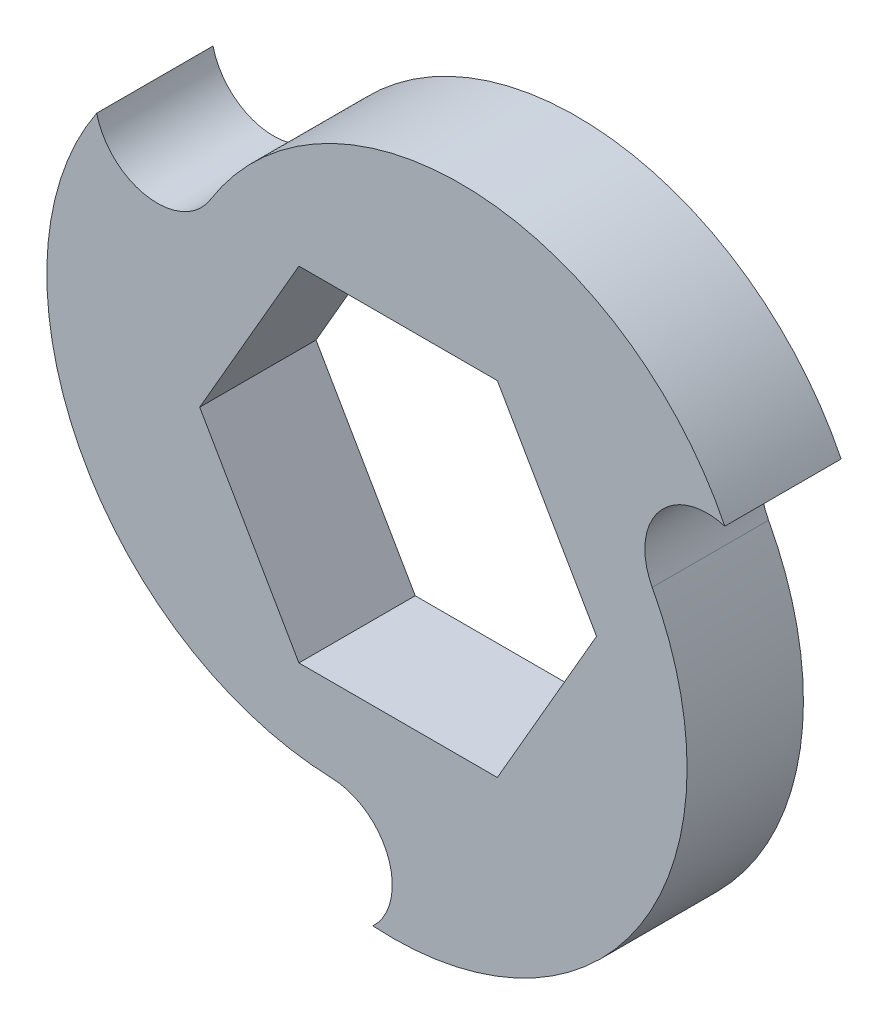
SolidWorks part; units mm, degrees
ref_plane "Front Plane" through (0, 0, 0) normal (0, 0, 1) x (1, 0, 0)
ref_plane "Top Plane" through (0, 0, 0) normal (0, 1, 0) x (1, 0, 0)
ref_plane "Right Plane" through (0, 0, 0) normal (1, 0, 0) x (0, 0, -1)
sketch "Sketch1" plane through (0, 0, 0) normal (0, 0, 1) x (1, 0, 0)
  line L6 (0, 0) -> (66.1503, 0) construction
  line L7 (7.5056, 0) -> (3.7528, 6.5)
  line L8 (3.7528, 6.5) -> (-3.7528, 6.5)
  line L9 (-3.7528, 6.5) -> (-7.5056, 0)
  line L10 (-7.5056, 0) -> (-3.7528, -6.5)
  line L11 (-3.7528, -6.5) -> (3.7528, -6.5)
  line L12 (3.7528, -6.5) -> (7.5056, 0)
  line L13 (0, 0) -> (-15.3926, 15.1529) construction
  line L14 (0, 0) -> (21.3672, 5.9055) construction
  circle A0 centre (0, 0) radius 13.75 construction
  arc A1 (271.8524, 134.8606) -> (128.8311, 107.2295) centre (210.3708, 69.1338) ccw construction
  arc A2 (101.7797, 101.1876) -> (128.8311, 107.2295) centre (112.9762, 114.637) ccw construction
  arc A3 (271.8524, 134.8606) -> (263.5592, 108.4124) centre (277.9018, 118.4394) ccw construction
  arc A4 (215.9777, -29.2632) -> (197.2195, -8.857) centre (198.7319, -26.2915) ccw construction
  arc A5 (215.9777, -29.2632) -> (263.5592, 108.4124) centre (189.7975, 56.8448) ccw construction
  arc A6 (101.7797, 101.1876) -> (197.2195, -8.857) centre (189.4416, 80.8063) ccw construction
  circle A7 centre (0, 0) radius 6.5 construction
  arc A8 (-7.1061, 6.9954) -> (12.3558, 6.033) centre (2.3581, 1.1198) cw
  arc A9 (12.3558, 6.033) -> (9.6113, 2.6564) centre (11.6908, 3.7698) ccw
  arc A10 (9.6113, 2.6564) -> (-0.9532, -13.7169) centre (-0.2093, -2.602) cw
  arc A11 (-0.9532, -13.7169) -> (-2.5052, -9.6518) centre (-2.5806, -12.0094) ccw
  arc A12 (-2.5052, -9.6518) -> (-11.4026, 7.6839) centre (-2.1488, 1.4823) cw
  arc A13 (-11.4026, 7.6839) -> (-7.1061, 6.9954) centre (-9.1102, 8.2396) ccw
  point P9 (95.6823, 117.3148)
  point P11 (128.6223, 31.4883)
  point P12 (212.2895, -27.5921)
  dimension "D1" = 27.5
  dimension "D2" = 120
  dimension "D3" = 13
  dimension "D4" = 3
extrude "Boss-Extrude1" add sketch "Sketch1" along normal blind 4.4
